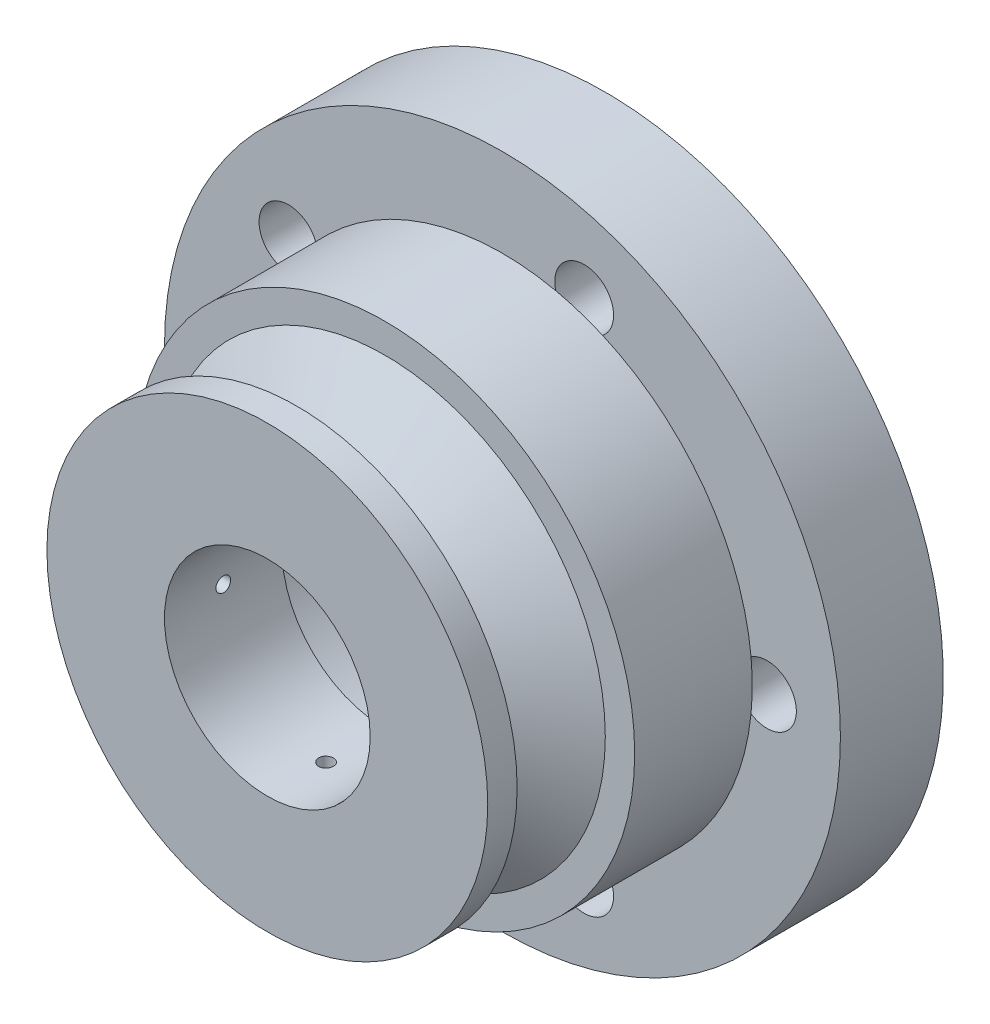
SolidWorks part; units mm, degrees
ref_plane "前视基准面" through (0, 0, 0) normal (0, 0, 1) x (1, 0, 0)
ref_plane "上视基准面" through (0, 0, 0) normal (0, 1, 0) x (1, 0, 0)
ref_plane "右视基准面" through (0, 0, 0) normal (1, 0, 0) x (0, 0, -1)
sketch "草图1" plane through (0, 0, 0) normal (0, 0, 1) x (1, 0, 0)
  circle A1 centre (0, 0) radius 11.5
  circle A2 centre (9, 0) radius 1
  circle A3 centre (2.7812, -8.5595) radius 1
  circle A4 centre (-7.2812, -5.2901) radius 1
  circle A5 centre (-7.2812, 5.2901) radius 1
  circle A6 centre (2.7812, 8.5595) radius 1
  circle A7 centre (0, 0) radius 6
  point P15 (0, 0)
extrude "凸台-拉伸1" add sketch "草图1" along normal blind 2.5
sketch "草图2" plane through (0, 0, 2.5) normal (0, 0, 1) x (1, 0, 0)
  circle A0 centre (0, 0) radius 8.5
  circle A1 centre (0, 0) radius 6
extrude "凸台-拉伸2" add sketch "草图2" along normal blind 4
sketch "草图3" plane through (0, 0, 6.5) normal (0, 0, 1) x (1, 0, 0)
  circle A0 centre (0, 0) radius 7.5
extrude "凸台-拉伸3" add sketch "草图3" along normal blind 4
sketch "草图4" plane through (0, 0, 10.5) normal (0, 0, 1) x (1, 0, 0)
  circle A0 centre (0, 0) radius 3.5
extrude "切除-拉伸1" cut sketch "草图4" against normal blind 4
sketch "草图5" plane through (0, 0, 0) normal (1, 0, 0) x (0, 0, -1)
  line L0 (-10.5, 0) -> (-6.7363, 0) construction
  line L1 (-10.5, 7.5) -> (-10.5, -7.5) construction
  line L2 (-6.5, 7.5) -> (-10.5, 7.5) construction
  line L3 (-7.5, 7.5) -> (-9.5, 7.5)
  line L5 (-8.25, 4.5) -> (-6.5, 7.5)
  line L6 (-8.75, 4.5) -> (-8.25, 4.5)
  line L8 (-8.75, 4.5) -> (-9.5, 7.5)
  line L9 (-6.5, 8.5) -> (-6.5, -8.5) construction
  line L10 (-6.5, 7.5) -> (-6.5, -7.5) construction
  line L11 (-6.5, 7.5) -> (-7.5, 7.5)
revolve "切除-旋转2" cut sketch "草图5" angle 360 about L0
sketch "草图6" plane through (0, 0, 0) normal (0, 1, 0) x (1, 0, 0)
  circle A0 centre (0, -8.5) radius 0.25
extrude "切除-拉伸2" cut sketch "草图6" against normal blind 14
sketch "草图7" plane through (0, 0, 0) normal (0, 0, -1) x (-1, 0, 0)
  circle A0 centre (-2.7812, -8.5595) radius 1 construction
  circle A1 centre (0, 0) radius 11.5
  circle A2 centre (0, 0) radius 11.5
  circle A3 centre (7.2812, -5.2901) radius 1 construction
  circle A4 centre (7.2812, 5.2901) radius 1 construction
  circle A5 centre (-2.7812, 8.5595) radius 1 construction
  circle A6 centre (-9, 0) radius 1 construction
  arc A7 (-8.4583, -0.8406) -> (-8.4583, 0.8406) centre (-9, 0) ccw construction
  circle A8 centre (-2.7812, -8.5595) radius 1
  circle A9 centre (7.2812, -5.2901) radius 1
  circle A10 centre (7.2812, 5.2901) radius 1
  circle A11 centre (-2.7812, 8.5595) radius 1
  circle A12 centre (-9, 0) radius 1
  arc A13 (-8.4583, -0.8406) -> (-8.4583, 0.8406) centre (-9, 0) ccw
  circle A14 centre (0, 0) radius 6 construction
  circle A15 centre (0, 0) radius 6
  circle M3 centre (0, 0) radius 11.5
  circle M4 centre (0, 0) radius 6
  circle M5 centre (-9, 0) radius 1
  circle M6 centre (-2.7812, -8.5595) radius 1
  circle M7 centre (7.2812, -5.2901) radius 1
  circle M8 centre (7.2812, 5.2901) radius 1
  circle M9 centre (-2.7812, 8.5595) radius 1
  dimension "D1" = 0
extrude "凸台-拉伸4" add sketch "草图7" along normal blind 1 contours A12 M3 M4 M6 M8 M9 M7 M5
sketch "草图8" plane through (0, 0, 10.5) normal (0, 0, 1) x (1, 0, 0)
  line L1 (0, -7.5) -> (0.4997, -7.4833)
  line L2 (0.4997, -7.4833) -> (0, -4.7)
  line L3 (-0.4997, -7.4833) -> (0, -4.7)
  line L4 (0, -7.5) -> (-0.4997, -7.4833)
  circle A1 centre (0, 0) radius 7.5 construction
  circle A2 centre (0, 0) radius 7.5 construction
  arc A3 (-0.4997, -7.4833) -> (0.4997, -7.4833) centre (0, 0) ccw
sketch "草图9" plane through (0, 0, 0) normal (1, 0, 0) x (0, 0, -1)
  circle A0 centre (-8.5, 0) radius 0.25
extrude "切除-拉伸8" cut sketch "草图9" against normal blind 12.2
